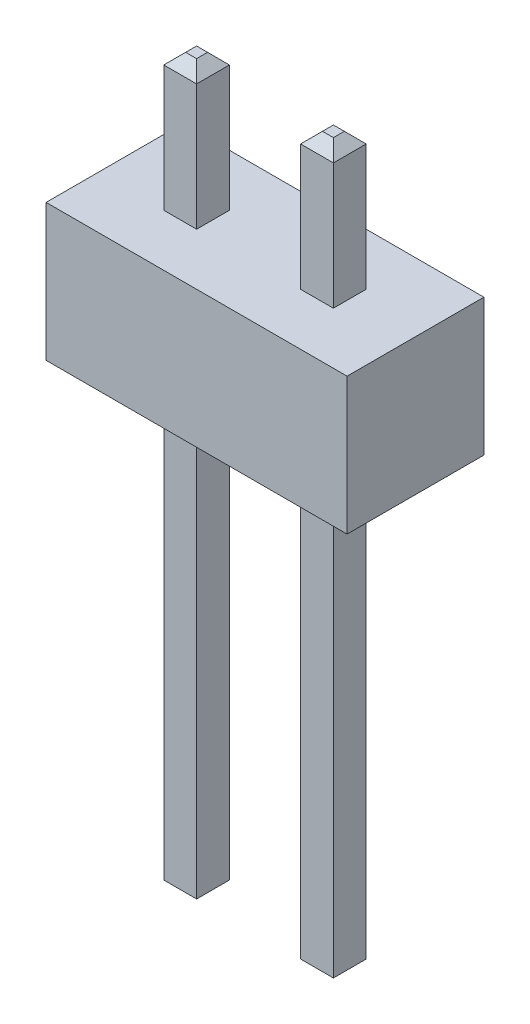
SolidWorks part; units mm, degrees
ref_plane "Front Plane" through (0, 0, 0) normal (0, 0, 1) x (1, 0, 0)
ref_plane "Top Plane" through (0, 0, 0) normal (0, 1, 0) x (1, 0, 0)
ref_plane "Right Plane" through (0, 0, 0) normal (1, 0, 0) x (0, 0, -1)
sketch "Sketch1" plane through (0, 0, 0) normal (0, 1, 0) x (1, 0, 0)
  line L0 (0, 1.25) -> (0, -1.25) construction
  line L1 (-2.75, 1.25) -> (2.75, 1.25)
  line L2 (-2.75, 1.25) -> (-2.75, -1.25)
  line L3 (-2.75, -1.25) -> (2.75, -1.25)
  line L4 (2.75, 1.25) -> (2.75, -1.25)
  dimension "D1" = 5.5
  dimension "D2" = 2.5
extrude "Boss-Extrude1" add sketch "Sketch1" along normal blind 2.5
sketch "Sketch2" plane through (0, 2.5, 0) normal (0, 1, 0) x (1, 0, 0)
  line L0 (0, 1.25) -> (0, -1.25) construction
  line L1 (2.75, 1.25) -> (-2.75, 1.25) construction
  line L2 (-2.75, -1.25) -> (2.75, -1.25) construction
  line L3 (0, 0) -> (-2.75, 0) construction
  line L4 (-2.75, 1.25) -> (-2.75, -1.25) construction
  line L5 (0, 0) -> (2.75, 0) construction
  line L6 (2.75, -1.25) -> (2.75, 1.25) construction
  line L7 (-1.25, 0.3) -> (-1.25, -0.3) construction
  line L8 (-1.55, 0.3) -> (-0.95, 0.3)
  line L9 (-1.55, 0.3) -> (-1.55, -0.3)
  line L10 (-1.55, -0.3) -> (-0.95, -0.3)
  line L11 (-0.95, 0.3) -> (-0.95, -0.3)
  point P18 (-1.25, 0)
  dimension "D1" = 1.25
  dimension "D2" = 0.6
  dimension "D3" = 0.6
extrude "Boss-Extrude2" add sketch "Sketch2" along normal blind 2.5 and the other way blind 10.8
chamfer "Chamfer1" distance 0.2 angle 45 8 edges at (-1.25, 5, -0.3) (-1.55, 5, 0) (-1.25, 5, 0.3) (-0.95, 5, 0) (-1.55, -8.3, 0) (-1.25, -8.3, -0.3) (-0.95, -8.3, 0) (-1.25, -8.3, 0.3)
mirror "Mirror1" about plane through (0, 0, 0) normal (1, 0, 0) of "Chamfer1", "Boss-Extrude2"
